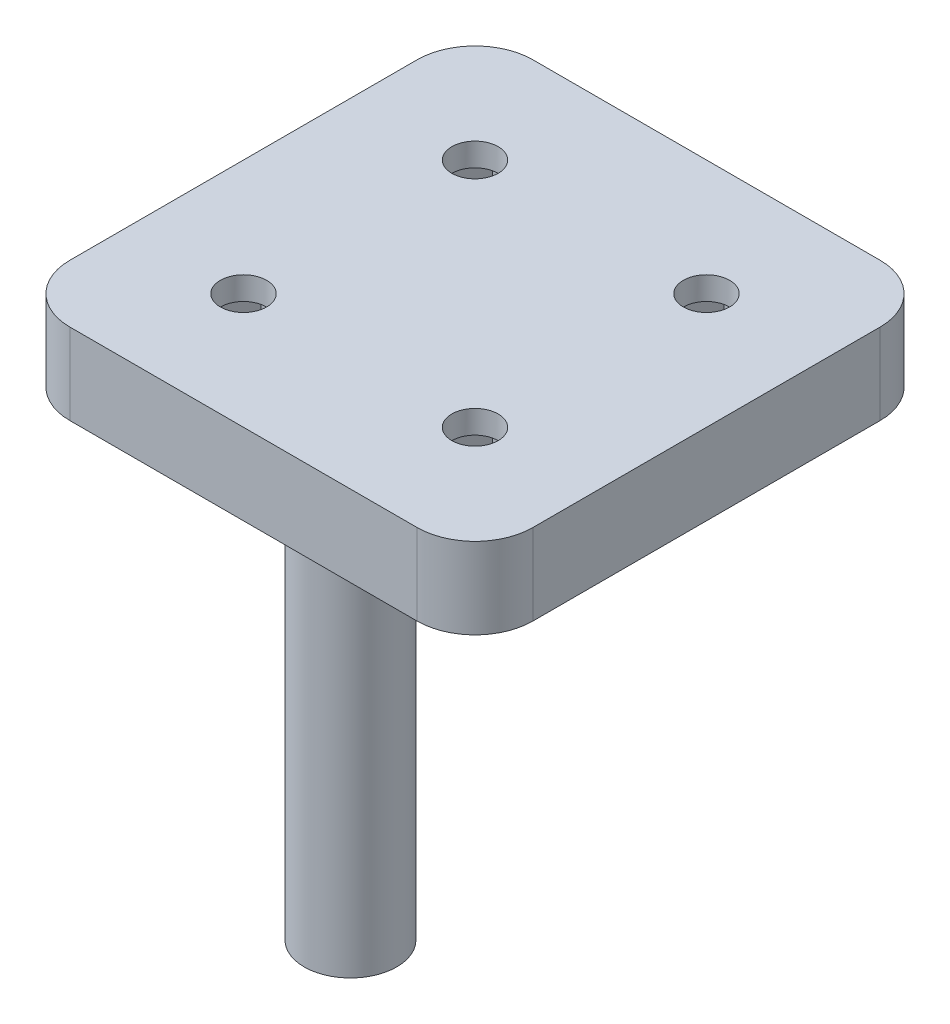
SolidWorks part; units mm, degrees
ref_plane "Front Plane" through (0, 0, 0) normal (0, 0, 1) x (1, 0, 0)
ref_plane "Top Plane" through (0, 0, 0) normal (0, 1, 0) x (1, 0, 0)
ref_plane "Right Plane" through (0, 0, 0) normal (1, 0, 0) x (0, 0, -1)
sketch "Sketch1" plane through (0, 0, 0) normal (0, 1, 0) x (1, 0, 0)
  line L1 (-20, -20) -> (20, -20)
  line L2 (-20, -20) -> (-20, 20)
  line L3 (-20, 20) -> (20, 20)
  line L4 (20, -20) -> (20, 20)
  line L5 (0, 20) -> (0, -20) construction
  line L6 (-20, 0) -> (20, 0) construction
  point P0 (0, 0)
  dimension "D1" = 40
  dimension "D2" = 40
extrude "Boss-Extrude1" add sketch "Sketch1" along normal blind 7
sketch "Sketch2" plane through (0, 0, 0) normal (0, 1, 0) x (1, 0, 0)
  line L1 (-10, -10) -> (10, -10)
  line L2 (-10, -10) -> (-10, 10)
  line L3 (-10, 10) -> (10, 10)
  line L4 (10, -10) -> (10, 10)
  line L5 (0, 10) -> (0, -10) construction
  line L6 (-10, 0) -> (10, 0) construction
  line L7 (-5.8431, 10) -> (-7.9215, 13.6)
  line L8 (-7.9215, 13.6) -> (-12.0785, 13.6)
  line L9 (-12.0785, 13.6) -> (-14.1569, 10)
  line L10 (-14.1569, 10) -> (-12.0785, 6.4)
  line L11 (-12.0785, 6.4) -> (-7.9215, 6.4)
  line L12 (-7.9215, 6.4) -> (-5.8431, 10)
  line L13 (14.1569, 10) -> (12.0785, 13.6)
  line L14 (12.0785, 13.6) -> (7.9215, 13.6)
  line L15 (7.9215, 13.6) -> (5.8431, 10)
  line L16 (5.8431, 10) -> (7.9215, 6.4)
  line L17 (7.9215, 6.4) -> (12.0785, 6.4)
  line L18 (12.0785, 6.4) -> (14.1569, 10)
  line L19 (-5.8431, -10) -> (-7.9215, -6.4)
  line L20 (-7.9215, -6.4) -> (-12.0785, -6.4)
  line L21 (-12.0785, -6.4) -> (-14.1569, -10)
  line L22 (-14.1569, -10) -> (-12.0785, -13.6)
  line L23 (-12.0785, -13.6) -> (-7.9215, -13.6)
  line L24 (-7.9215, -13.6) -> (-5.8431, -10)
  line L25 (14.1569, -10) -> (12.0785, -6.4)
  line L26 (12.0785, -6.4) -> (7.9215, -6.4)
  line L27 (7.9215, -6.4) -> (5.8431, -10)
  line L28 (5.8431, -10) -> (7.9215, -13.6)
  line L29 (7.9215, -13.6) -> (12.0785, -13.6)
  line L30 (12.0785, -13.6) -> (14.1569, -10)
  circle A4 centre (-10, 10) radius 3.6 construction
  circle A5 centre (10, 10) radius 3.6 construction
  circle A6 centre (-10, -10) radius 3.6 construction
  circle A7 centre (10, -10) radius 3.6 construction
  point P0 (0, 0)
  dimension "D3" = 7.2
  dimension "D1" = 20
  dimension "D2" = 20
sketch "Sketch3" plane through (0, 7, 0) normal (0, 1, 0) x (1, 0, 0)
  circle A0 centre (-10, 10) radius 2
  circle A1 centre (10, 10) radius 2
  circle A2 centre (-10, -10) radius 2
  circle A3 centre (10, -10) radius 2
  dimension "D1" = 4
extrude "Cut-Extrude2" cut sketch "Sketch3" against normal through all
fillet "Fillet1" radius 5 4 edges at (-20, 3.5, 20) (20, 3.5, 20) (20, 3.5, -20) (-20, 3.5, -20)
sketch "Sketch4" plane through (0, 0, 0) normal (0, 1, 0) x (1, 0, 0)
  line L0 (0, 20) -> (0, -10.76) construction
  line L1 (15, 20) -> (-15, 20) construction
  circle A0 centre (0, -10.76) radius 4
  dimension "D1" = 8
extrude "Cut-Extrude7" cut sketch "Sketch2" along normal blind 5 contours L24 L23 L22 L21 L20 L2 L1 | L30 L29 L28 L1 L4 L26 L25 | L27 L26 L4 L1 | L20 L19 L1 L2 | L11 L10 L9 L8 L7 L3 L2 | L12 L11 L2 L3 | L17 L16 L3 L4 | L18 L17 L4 L3 L15 L14 L13
extrude "Boss-Extrude2" add sketch "Sketch4" against normal blind 36
sketch "Sketch5" plane through (0, -36, 0) normal (0, -1, 0) x (-1, 0, 0)
  circle A0 centre (0, -10.76) radius 2
  dimension "D1" = 4
extrude "Cut-Extrude8" cut sketch "Sketch5" against normal blind 5
